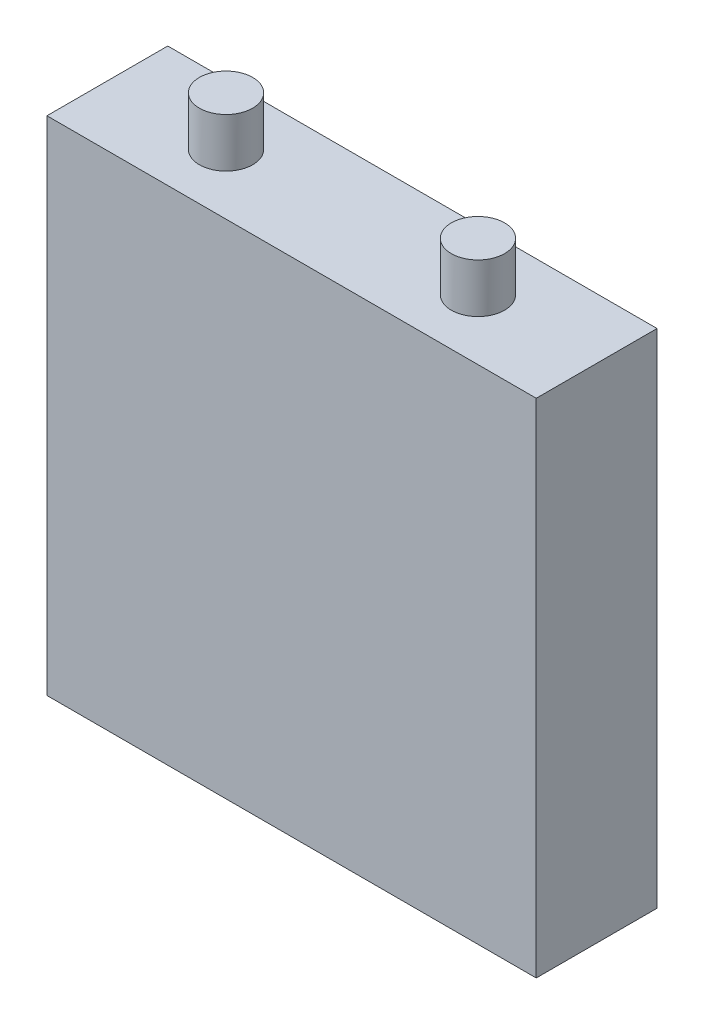
SolidWorks part; units mm, degrees
ref_plane "Front Plane" through (0, 0, 0) normal (0, 0, 1) x (1, 0, 0)
ref_plane "Top Plane" through (0, 0, 0) normal (0, 1, 0) x (1, 0, 0)
ref_plane "Right Plane" through (0, 0, 0) normal (1, 0, 0) x (0, 0, -1)
sketch "Sketch1" plane through (0, 0, 0) normal (0, 1, 0) x (1, 0, 0)
  line L1 (0, 0) -> (137.7, 0)
  line L2 (0, 0) -> (0, 34)
  line L3 (0, 34) -> (137.7, 34)
  line L4 (137.7, 0) -> (137.7, 34)
  dimension "D1" = 34
  dimension "D2" = 137.7
extrude "Boss-Extrude1" add sketch "Sketch1" along normal blind 141.3
sketch "Sketch2" plane through (0, 141.3, 0) normal (0, 1, 0) x (1, 0, 0)
  line L0 (0, 0) -> (137.7, 0) construction
  line L1 (137.7, 34) -> (0, 34) construction
  circle A0 centre (33.4, 17) radius 7.5
  circle A1 centre (104.3, 17) radius 7.5
  point P4 (21.6154, 17)
  point P5 (105.425, 17)
  point P6 (0, 0)
  point P9 (0, 0)
  point P12 (68.85, 34)
  dimension "D1" = 15
  dimension "D2" = 15
  dimension "D3" = 17
  dimension "D4" = 35.45
  dimension "D5" = 70.9
extrude "Boss-Extrude2" add sketch "Sketch2" along normal blind 13.8
